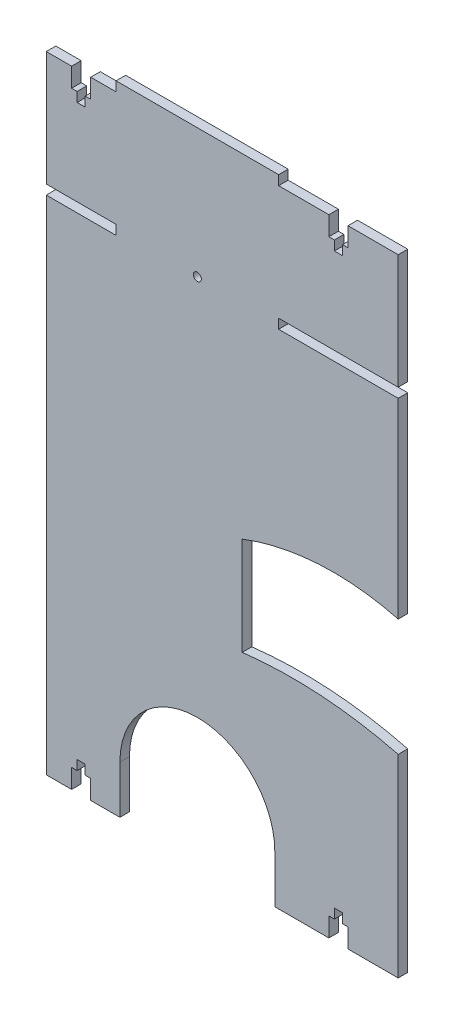
SolidWorks part; units mm, degrees
ref_plane "Front Plane" through (0, 0, 0) normal (0, 0, 1) x (1, 0, 0)
ref_plane "Top Plane" through (0, 0, 0) normal (0, 1, 0) x (1, 0, 0)
ref_plane "Right Plane" through (0, 0, 0) normal (1, 0, 0) x (0, 0, -1)
sketch "Sketch2" plane through (0, 0, 0) normal (0, 0, 1) x (1, 0, 0)
  line L1 (-92, 166.25) -> (92, 166.25)
  line L2 (-92, 166.25) -> (-92, -166.25)
  line L3 (-92, -166.25) -> (92, -166.25)
  line L4 (92, 166.25) -> (92, -166.25)
  line L5 (-92, 166.25) -> (92, -166.25) construction
  line L6 (-92, -166.25) -> (92, 166.25) construction
  point P0 (0, 0)
  dimension "D1" = 332.5
  dimension "D2" = 184
extrude "Boss-Extrude1" add sketch "Sketch2" along normal blind 5
sketch "Sketch3" plane through (0, 0, 5) normal (0, 0, 1) x (1, 0, 0)
  line L0 (-92, 166.25) -> (-92, -166.25) construction
  line L8 (92, -166.25) -> (92, 166.25) construction
  line L17 (29.5, 96.25) -> (92, 96.25) construction
  line L21 (-55.5, 161.25) -> (-92, 161.25)
  line L22 (-55.5, 161.25) -> (-55.5, 166.25)
  line L23 (-55.5, 166.25) -> (-92, 166.25)
  line L24 (-92, 161.25) -> (-92, 166.25)
  line L25 (-55.5, 161.25) -> (-92, 166.25) construction
  line L26 (-55.5, 166.25) -> (-92, 161.25) construction
  line L27 (29.5, 161.25) -> (92, 161.25)
  line L28 (29.5, 161.25) -> (29.5, 166.25)
  line L29 (29.5, 166.25) -> (92, 166.25)
  line L30 (92, 161.25) -> (92, 166.25)
  line L31 (29.5, 161.25) -> (92, 166.25) construction
  line L32 (29.5, 166.25) -> (92, 161.25) construction
  line L33 (29.5, 101.25) -> (92, 101.25)
  line L34 (27.5, -141.25) -> (27.5, -166.25)
  line L37 (-92, -166.25) -> (92, -166.25) construction
  line L38 (27.5, -166.25) -> (-53.5, -166.25)
  line L39 (-53.5, -166.25) -> (-53.5, -141.25)
  line L40 (29.5, 101.25) -> (29.5, 96.25)
  line L41 (29.5, 96.25) -> (92, 96.25)
  line L42 (92, 101.25) -> (92, 96.25)
  line L43 (29.5, 101.25) -> (92, 96.25) construction
  line L44 (29.5, 96.25) -> (92, 101.25) construction
  line L45 (-98, 101.25) -> (-55.5, 101.25) construction
  line L46 (-55.5, 96.25) -> (-92, 96.25)
  line L47 (-55.5, 96.25) -> (-55.5, 101.25)
  line L48 (-55.5, 101.25) -> (-92, 101.25)
  line L49 (-92, 96.25) -> (-92, 101.25)
  line L50 (-55.5, 96.25) -> (-92, 101.25) construction
  line L51 (-55.5, 101.25) -> (-92, 96.25) construction
  arc A2 (27.5, -141.25) -> (-53.5, -141.25) centre (-13, -141.25) ccw
  point P7 (-73.75, -98.75)
  point P17 (60.75, -98.75)
  point P32 (-73.75, 163.75)
  point P39 (60.75, 163.75)
  point P45 (60.75, 98.75)
  point P54 (-73.75, 98.75)
extrude "Cut-Extrude1" cut sketch "Sketch3" against normal blind 5
sketch "Sketch4" plane through (0, 0, 5) normal (0, 0, 1) x (1, 0, 0)
  line L0 (-73.75, 161.25) -> (-73.75, 123.1738) construction
  line L1 (-92, 161.25) -> (-55.5, 161.25) construction
  line L2 (69.7422, 161.25) -> (69.7422, -166.25) construction
  line L3 (-92, 131.25) -> (92, 131.25) construction
  line L5 (-13, 166.25) -> (-13, 111.1543) construction
  line L6 (29.5, 166.25) -> (-55.5, 166.25) construction
  line L7 (29.5, 161.25) -> (92, 161.25) construction
  line L8 (27.5, -166.25) -> (92, -166.25) construction
  line L9 (69.7422, -2.5) -> (44.3363, -2.5) construction
  line L10 (92, 101.25) -> (92, 161.25) construction
  line L11 (0, 131.25) -> (0, 111.1543) construction
  line L12 (0, 111.1543) -> (-13, 111.1543) construction
  line L13 (-6.5, 111.1543) -> (-6.5, 119.3244) construction
  line L14 (60.75, 161.25) -> (60.75, 140.689) construction
  line L15 (55.75, 161.25) -> (55.75, 151.25)
  line L16 (55.75, 151.25) -> (58.65, 151.25)
  line L17 (58.65, 151.25) -> (58.65, 146.25)
  line L18 (58.65, 146.25) -> (62.85, 146.25)
  line L19 (55.75, 161.25) -> (65.75, 161.25)
  line L20 (62.85, 151.25) -> (62.85, 146.25)
  line L21 (65.75, 151.25) -> (62.85, 151.25)
  line L22 (65.75, 161.25) -> (65.75, 151.25)
  line L23 (-78.75, 161.25) -> (-78.75, 151.25)
  line L24 (-78.75, 151.25) -> (-75.85, 151.25)
  line L25 (-75.85, 151.25) -> (-75.85, 146.25)
  line L26 (-68.75, 161.25) -> (-78.75, 161.25)
  line L27 (-71.65, 146.25) -> (-75.85, 146.25)
  line L28 (-71.65, 151.25) -> (-71.65, 146.25)
  line L29 (-68.75, 151.25) -> (-71.65, 151.25)
  line L30 (-68.75, 161.25) -> (-68.75, 151.25)
  line L31 (60.75, -166.25) -> (60.75, -145.689) construction
  line L32 (65.75, -166.25) -> (65.75, -156.25)
  line L33 (65.75, -156.25) -> (62.85, -156.25)
  line L34 (62.85, -156.25) -> (62.85, -151.25)
  line L35 (55.75, -166.25) -> (65.75, -166.25)
  line L36 (58.65, -151.25) -> (62.85, -151.25)
  line L37 (58.65, -156.25) -> (58.65, -151.25)
  line L38 (55.75, -156.25) -> (58.65, -156.25)
  line L39 (55.75, -166.25) -> (55.75, -156.25)
  line L40 (-68.75, -166.25) -> (-68.75, -156.25)
  line L41 (-68.75, -156.25) -> (-71.65, -156.25)
  line L42 (-71.65, -156.25) -> (-71.65, -151.25)
  line L43 (-71.65, -151.25) -> (-75.85, -151.25)
  line L44 (-68.75, -166.25) -> (-78.75, -166.25)
  line L45 (-75.85, -156.25) -> (-75.85, -151.25)
  line L46 (-78.75, -156.25) -> (-75.85, -156.25)
  line L47 (-78.75, -166.25) -> (-78.75, -156.25)
  point P36 (60.75, 146.25)
  point P46 (-73.75, 146.25)
  point P57 (60.75, -151.25)
  point P66 (-73.75, -151.25)
  dimension "D1" = 10
  dimension "D2" = 5
  dimension "D3" = 2.9
  dimension "D4" = 5
extrude "Cut-Extrude2" cut sketch "Sketch4" against normal blind 10
sketch "Sketch5" plane through (0, 0, 5) normal (0, 0, 1) x (1, 0, 0)
  line L0 (-55.5, 98.75) -> (29.5, 98.75) construction
  line L1 (-55.5, 96.25) -> (-55.5, 101.25) construction
  line L2 (29.5, 96.25) -> (29.5, 101.25) construction
  circle A0 centre (-13, 98.75) radius 2.1
  dimension "D1" = 4.2
extrude "Cut-Extrude3" cut sketch "Sketch5" against normal blind 10
sketch "Sketch6" plane through (0, 0, 0) normal (0, 0, -1) x (-1, 0, 0)
  line L0 (-78.2, -106.25) -> (-41.2, -106.25)
  line L1 (-41.2, -106.25) -> (-40.7, -106.25)
  line L2 (-39.7, -107.25) -> (-39.7, -125.25)
  line L3 (-40.7, -126.25) -> (-78.7, -126.25)
  line L4 (-79.7, -125.25) -> (-79.7, -107.25)
  line L5 (-78.7, -106.25) -> (-78.2, -106.25)
  circle A0 centre (-35.2, -111.17) radius 2.5
  circle A1 centre (-35.2, -121.33) radius 2.5
  circle A2 centre (-84.2, -111.17) radius 2.5
  circle A3 centre (-84.2, -121.33) radius 2.5
  arc A4 (-40.7, -106.25) -> (-39.7, -107.25) centre (-40.7, -107.25) cw
  arc A5 (-39.7, -125.25) -> (-40.7, -126.25) centre (-40.7, -125.25) cw
  arc A6 (-78.7, -126.25) -> (-79.7, -125.25) centre (-78.7, -125.25) cw
  arc A7 (-79.7, -107.25) -> (-78.7, -106.25) centre (-78.7, -107.25) cw
extrude "Cut-Extrude4" [suppressed] cut sketch "Sketch6" against normal blind 20
sketch "Sketch7" plane through (0, 0, 5) normal (0, 0, 1) x (1, 0, 0)
  line L4 (92.0183, -3.9595) -> (92, -22.8853)
  line L5 (92, -166.25) -> (92, 96.25) construction
  arc A4 (92.0183, -3.9595) -> (39.9761, 3.3554) centre (49.7, -116.25) ccw
  arc A5 (92, -22.8853) -> (36.0805, -14.6589) centre (49.7, -116.25) ccw
  arc A6 (39.9761, 3.3554) -> (36.0805, -14.6589) centre (102.0215, -19.4902) ccw
extrude "Cut-Extrude6" [suppressed] cut sketch "Sketch7" against normal through all
sketch "Esquisse2" plane through (0, 0, 5) normal (0, 0, 1) x (1, 0, 0)
  line L0 (92, -59.5677) -> (10.4707, -59.5677) construction
  line L1 (10.4707, -8.2738) -> (10.4707, -59.5677)
  line L2 (92, -3.7504) -> (92, -64.9958)
  arc A0 (10.4707, -59.5677) -> (92, -64.9958) centre (36.6049, -282.026) cw
  arc A1 (10.4707, -8.2738) -> (92, -3.7504) centre (58.2719, -132.8388) cw
  point P3 (92, -57.1675)
extrude "Enlèv. mat.-Extru.2" cut sketch "Esquisse2" against normal blind 10
